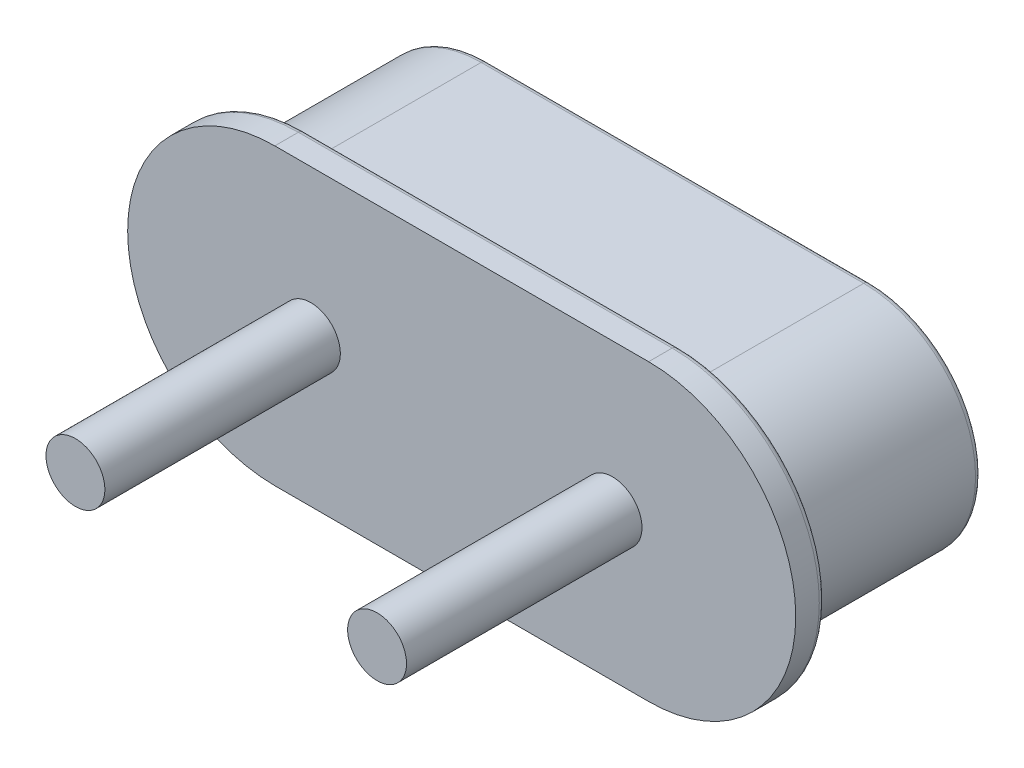
SolidWorks part; units mm, degrees
ref_plane "Front Plane" through (0, 0, 0) normal (0, 0, 1) x (1, 0, 0)
ref_plane "Top Plane" through (0, 0, 0) normal (0, 1, 0) x (1, 0, 0)
ref_plane "Right Plane" through (0, 0, 0) normal (1, 0, 0) x (0, 0, -1)
sketch "Sketch1" plane through (0, 0, 0) normal (0, 0, 1) x (1, 0, 0)
  line L0 (-3.175, 0) -> (3.175, 0) construction
  line L1 (-3.175, 2.5) -> (3.175, 2.5)
  line L2 (-3.175, -2.5) -> (3.175, -2.5)
  line L3 (-5.675, 0) -> (-5.675, 3.336) construction
  line L4 (5.675, 0) -> (5.675, 4.4657) construction
  arc A0 (-3.175, 2.5) -> (-3.175, -2.5) centre (-3.175, 0) ccw
  arc A1 (3.175, -2.5) -> (3.175, 2.5) centre (3.175, 0) ccw
  point P2 (0, 0)
  dimension "D1" = 11.35
  dimension "5" = 5
extrude "Boss-Extrude1" add sketch "Sketch1" against normal blind 0.5
sketch "Sketch3" plane through (0, 0, -0.5) normal (0, 0, -1) x (-1, 0, 0)
  line L0 (-3.25, 0) -> (3.25, 0) construction
  line L1 (-3.25, 1.9) -> (3.25, 1.9)
  line L2 (-3.25, -1.9) -> (3.25, -1.9)
  line L3 (5.15, 0) -> (5.15, -4.1369) construction
  line L4 (-5.15, 0) -> (-5.15, -4.6545) construction
  arc A0 (-3.25, 1.9) -> (-3.25, -1.9) centre (-3.25, 0) ccw
  arc A1 (3.25, -1.9) -> (3.25, 1.9) centre (3.25, 0) ccw
  point P2 (0, 0)
  dimension "D1" = 10.3
  dimension "D2" = 3.8
extrude "Boss-Extrude2" add sketch "Sketch3" along normal blind 3.18
sketch "Sketch4" plane through (0, 0, 0) normal (0, 0, 1) x (1, 0, 0)
  circle A0 centre (-2.44, 0) radius 0.215
  circle A1 centre (2.44, 0) radius 0.215
  dimension "D1" = 0.43
  dimension "0.43" = 0.43
  dimension "D2" = 4.88
  dimension "D3" = 2.44
  dimension "D4" = 2.44
fillet "Fillet5" radius 0.1 4 edges at (-5.15, 0, -3.68) (0, -1.9, -3.68) (5.15, 0, -3.68) (0, 1.9, -3.68)
fillet "Fillet6" radius 0.1 4 edges at (0, -2.5, -0.5) (-5.675, 0, -0.5) (0, 2.5, -0.5) (5.675, 0, -0.5)
sketch "Sketch7" plane through (0, 0, 0) normal (0, 0, 1) x (1, 0, 0)
  line L0 (0, 2.5) -> (0, -2.5) construction
  line L1 (3.175, 2.5) -> (-3.175, 2.5) construction
  line L2 (-3.175, -2.5) -> (3.175, -2.5) construction
  line L3 (-2.5623, 0) -> (2.5623, 0) construction
  circle A0 centre (2.5623, 0) radius 0.5
  circle A1 centre (-2.5623, 0) radius 0.5
  point P10 (0, 0)
  dimension "D2" = 1
  dimension "D1" = 2.5623
extrude "Boss-Extrude3" add sketch "Sketch7" along normal blind 4
sketch "Sketch8" plane through (0, 0, -3.68) normal (0, 0, -1) x (-1, 0, 0)
  text T0 "16.000" font "Century Gothic" height 1.5
extrude "Boss-Extrude4" add sketch "Sketch8" along normal blind 0.01
